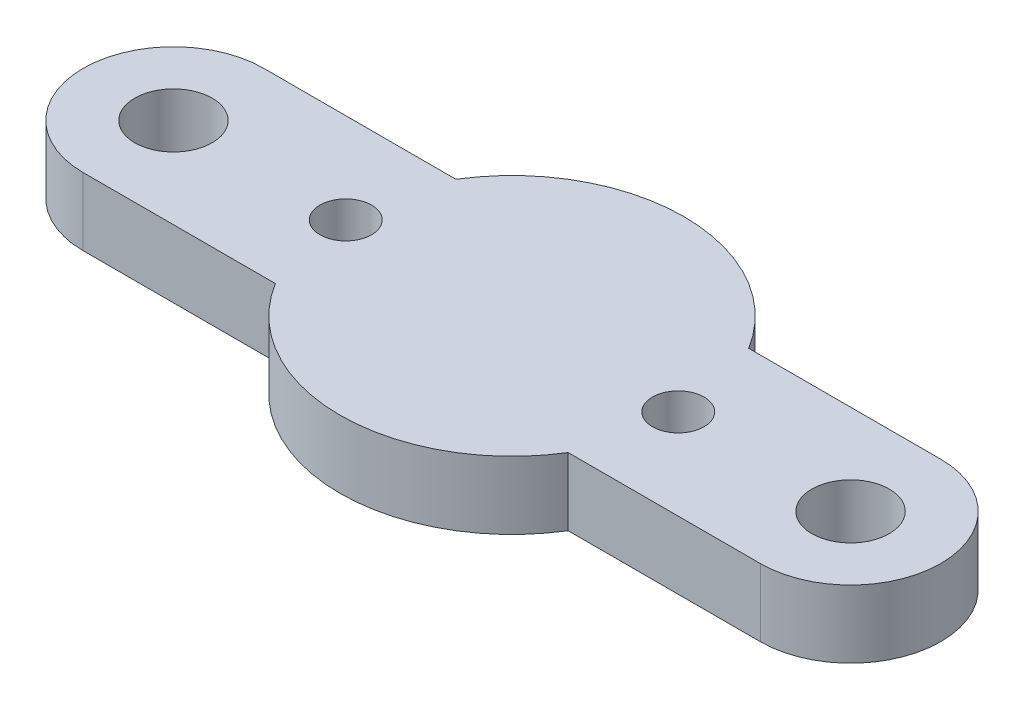
SolidWorks part; units mm, degrees
ref_plane "Front" through (0, 0, 0) normal (0, 0, 1) x (1, 0, 0)
ref_plane "Top" through (0, 0, 0) normal (0, 1, 0) x (1, 0, 0)
ref_plane "Right" through (0, 0, 0) normal (1, 0, 0) x (0, 0, -1)
sketch "Sketch1" plane through (0, 0, 0) normal (0, 1, 0) x (1, 0, 0)
  line L0 (-7.366, 0) -> (7.366, 0) construction
  line L1 (-15, 0) -> (15, 0) construction
  line L2 (-15, 4) -> (-6.4857, 4)
  line L3 (-15, -4) -> (-6.4857, -4)
  line L4 (6.4857, 4) -> (15, 4)
  line L5 (6.4857, -4) -> (15, -4)
  circle A0 centre (-7.366, 0) radius 1.143
  circle A1 centre (7.366, 0) radius 1.143
  arc A2 (-15, 4) -> (-15, -4) centre (-15, 0) ccw
  arc A3 (15, -4) -> (15, 4) centre (15, 0) ccw
  circle A4 centre (-15, 0) radius 1.7145
  circle A5 centre (15, 0) radius 1.7145
  arc A6 (6.4857, 4) -> (-6.4857, 4) centre (0, 0) ccw
  arc A7 (-6.4857, -4) -> (6.4857, -4) centre (0, 0) ccw
  point P7 (0, 0)
  dimension "D1" = 2.286
  dimension "D3" = 3.429
  dimension "D6" = 7.62
  dimension "D2" = 14.732
  dimension "D4" = 30
  dimension "D5" = 8
extrude "Boss-Extrude1" add sketch "Sketch1" along normal blind 3
